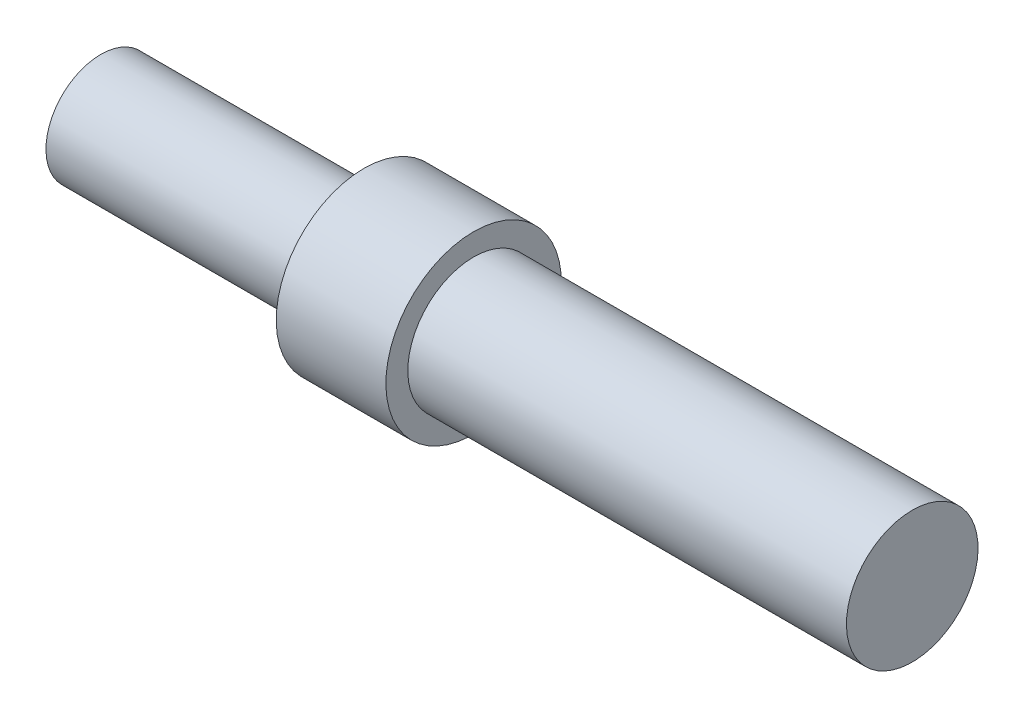
SolidWorks part; units mm, degrees
ref_plane "Front Plane" through (0, 0, 0) normal (0, 0, 1) x (1, 0, 0)
ref_plane "Top Plane" through (0, 0, 0) normal (0, 1, 0) x (1, 0, 0)
ref_plane "Right Plane" through (0, 0, 0) normal (1, 0, 0) x (0, 0, -1)
sketch "Sketch1" plane through (0, 0, 0) normal (0, 0, 1) x (1, 0, 0)
  line L0 (0, 0) -> (0, 1.25)
  line L1 (0, 1.25) -> (6, 1.25)
  line L2 (6, 1.25) -> (6, 2)
  line L3 (6, 2) -> (8.5, 2)
  line L4 (8.5, 2) -> (8.5, 1.5)
  line L5 (8.5, 1.5) -> (18.5, 1.5)
  line L6 (18.5, 1.5) -> (18.5, 0)
  line L7 (18.5, 0) -> (0, 0)
  dimension "D1" = 1.25
  dimension "D2" = 6
  dimension "D3" = 2
  dimension "D4" = 1.5
  dimension "D5" = 2.5
  dimension "D6" = 10
revolve "Revolve1" add sketch "Sketch1" angle 360 about L7
